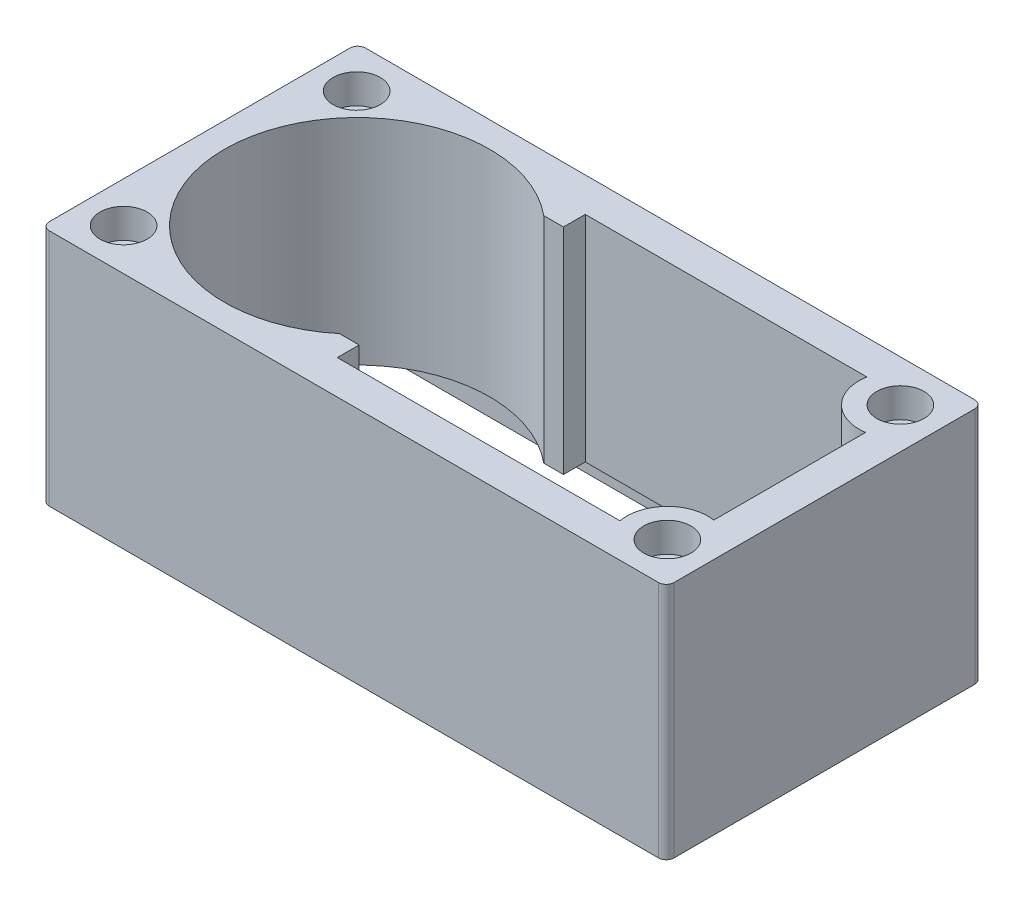
SolidWorks part; units mm, degrees
ref_plane "Front Plane" through (0, 0, 0) normal (0, 0, 1) x (1, 0, 0)
ref_plane "Top Plane" through (0, 0, 0) normal (0, 1, 0) x (1, 0, 0)
ref_plane "Right Plane" through (0, 0, 0) normal (1, 0, 0) x (0, 0, -1)
sketch "Sketch1" plane through (0, 0, 0) normal (0, 1, 0) x (1, 0, 0)
  line L1 (-20.193, 10.2235) -> (20.193, 10.2235)
  line L2 (-20.193, 10.2235) -> (-20.193, -10.2235)
  line L3 (-20.193, -10.2235) -> (20.193, -10.2235)
  line L4 (20.193, 10.2235) -> (20.193, -10.2235)
  line L5 (-20.193, 10.2235) -> (20.193, -10.2235) construction
  line L6 (-20.193, -10.2235) -> (20.193, 10.2235) construction
  point P0 (0, 0)
  dimension "D1" = 40.386
  dimension "D2" = 20.447
extrude "Boss-Extrude1" add sketch "Sketch1" along normal blind 15.4178
fillet "Fillet1" radius 0.508 4 edges at (20.193, 7.7089, 10.2235) (20.193, 7.7089, -10.2235) (-20.193, 7.7089, -10.2235) (-20.193, 7.7089, 10.2235)
hole_wizard "#2 Clearance Hole1" positions "Sketch4" profile "Sketch5" hole size "#2" standard "ANSI Inch" end condition up to next
sketch "Sketch4" plane through (0, 15.4178, 0) normal (0, 1, 0) x (1, 0, 0)
  line L1 (-17.5704, 7.5311) -> (17.5704, 7.5311)
  line L2 (-17.5704, 7.5311) -> (-17.5704, -7.5311)
  line L3 (-17.5704, -7.5311) -> (17.5704, -7.5311)
  line L4 (17.5704, 7.5311) -> (17.5704, -7.5311)
  line L5 (-17.5704, 7.5311) -> (17.5704, -7.5311) construction
  line L6 (-17.5704, -7.5311) -> (17.5704, 7.5311) construction
  point P2 (17.5704, -7.5311)
  point P81 (-17.5704, 7.5311)
  point P82 (-17.5704, -7.5311)
  point P83 (17.5704, 7.5311)
  point P97 (0, 0)
  dimension "D1" = 15.0622
  dimension "D2" = 35.1409
sketch "Sketch5" plane through (17.5704, 15.4178, 7.5311) normal (1, 0, 0) x (0, 0, 1)
  line L0 (0, 0) -> (0, 15.4178)
  line L1 (0, 15.4178) -> (1.1303, 15.4178)
  line L2 (1.1303, 15.4178) -> (1.1303, 0)
  line L5 (1.1303, 0) -> (0, 0)
  line L11 (0, -6.35) -> (0, 107.95) construction
  dimension "Thru Hole Dia." = 2.2606
  dimension "Thru Hole Depth" = 15.4178
sketch "Sketch6" plane through (0, 15.4178, 0) normal (0, 1, 0) x (1, 0, 0)
  circle A0 centre (-10.0147, 0) radius 8.5725
  circle A2 centre (-17.5704, 7.5311) radius 1.1303 construction
  dimension "D1" = 17.145
  dimension "D2" = 10.668
sketch "Sketch8" plane through (0, 15.4178, 0) normal (0, 1, 0) x (1, 0, 0)
  circle A0 centre (-17.5704, -7.5311) radius 1.524
  circle A1 centre (-17.5704, 7.5311) radius 1.524
  circle A2 centre (17.5704, 7.5311) radius 1.524
  circle A3 centre (17.5704, -7.5311) radius 1.524
  dimension "D1" = 3.048
extrude "Cut-Extrude2" cut sketch "Sketch8" against normal blind 1.905
sketch "Sketch10" plane through (0, 15.4178, 0) normal (0, 1, 0) x (1, 0, 0)
  line L0 (-4.5489, 6.604) -> (-4.5489, -6.604)
  line L1 (-4.5489, -6.604) -> (-3.2789, -6.604)
  line L2 (-3.2789, -6.604) -> (-3.2789, -8.0137)
  line L3 (-3.2789, -8.0137) -> (14.9927, -8.0137)
  line L5 (17.9835, -4.9413) -> (17.9835, 4.8706)
  line L7 (14.9217, 8.0137) -> (-3.2789, 8.0137)
  line L8 (-3.2789, 8.0137) -> (-3.2789, 6.604)
  line L9 (-3.2789, 6.604) -> (-4.5489, 6.604)
  line L10 (20.193, -9.7155) -> (20.193, 9.7155) construction
  line L11 (19.685, 10.2235) -> (-19.685, 10.2235) construction
  line L12 (5.8214, 8.0137) -> (5.8214, 10.2235) construction
  line L14 (17.9835, -0.0354) -> (20.193, 0) construction
  arc A2 (14.9217, 8.0137) -> (17.9835, 4.8706) centre (17.5704, 7.5311) ccw
  arc A3 (17.9835, -4.9413) -> (14.9927, -8.0137) centre (17.5704, -7.5311) ccw
  circle A4 centre (-10.0147, 0) radius 8.5725 construction
  point P2 (0, 0)
  point P3 (-1.7525, 5.4229)
  point P26 (0, 0)
  point P27 (0, 0)
  dimension "D1" = 13.208
  dimension "D2" = 2.2098
  dimension "D4" = 1.27
extrude "Cut-Extrude5" cut sketch "Sketch6" against normal through all contours A0
extrude "Cut-Extrude6" cut sketch "Sketch10" against normal through all contours L0 L1 L2 L3 A3 L5 A2 L7 L8 L9
sketch "Sketch11" plane through (0, 0, 0) normal (0, -1, 0) x (1, 0, 0)
  line L0 (18.9611, 8.9916) -> (-18.9611, 8.9916)
  line L1 (-18.9611, 8.9916) -> (-18.9611, -8.9916)
  line L2 (-18.9611, -8.9916) -> (18.9611, -8.9916)
  line L3 (18.9611, -8.9916) -> (18.9611, 8.9916)
  line L4 (20.193, -9.7155) -> (20.193, 9.7155)
  line L5 (19.685, 10.2235) -> (-19.685, 10.2235)
  line L6 (-20.193, 9.7155) -> (-20.193, -9.7155)
  line L7 (-19.685, -10.2235) -> (19.685, -10.2235)
  line L8 (20.193, -9.7155) -> (20.193, 9.7155)
  line L9 (19.685, 10.2235) -> (-19.685, 10.2235)
  line L10 (-20.193, 9.7155) -> (-20.193, -9.7155)
  line L11 (-19.685, -10.2235) -> (19.685, -10.2235)
  arc A0 (-18.9611, 8.9916) -> (-18.9611, 8.9916) centre (-18.9611, 8.9916) ccw
  arc A1 (-18.9611, -8.9916) -> (-18.9611, -8.9916) centre (-18.9611, -8.9916) ccw
  arc A2 (18.9611, -8.9916) -> (18.9611, -8.9916) centre (18.9611, -8.9916) ccw
  arc A3 (18.9611, 8.9916) -> (18.9611, 8.9916) centre (18.9611, 8.9916) ccw
  arc A4 (20.193, 9.7155) -> (19.685, 10.2235) centre (19.685, 9.7155) ccw
  arc A5 (-19.685, 10.2235) -> (-20.193, 9.7155) centre (-19.685, 9.7155) ccw
  arc A6 (-20.193, -9.7155) -> (-19.685, -10.2235) centre (-19.685, -9.7155) ccw
  arc A7 (19.685, -10.2235) -> (20.193, -9.7155) centre (19.685, -9.7155) ccw
  arc A8 (20.193, 9.7155) -> (19.685, 10.2235) centre (19.685, 9.7155) ccw
  arc A9 (-19.685, 10.2235) -> (-20.193, 9.7155) centre (-19.685, 9.7155) ccw
  arc A10 (-20.193, -9.7155) -> (-19.685, -10.2235) centre (-19.685, -9.7155) ccw
  arc A11 (19.685, -10.2235) -> (20.193, -9.7155) centre (19.685, -9.7155) ccw
  point P24 (0, 0)
  line M11 (-3.2789, -8.0137) -> (-3.2789, -6.604)
  line M12 (-3.2789, -6.604) -> (-4.5489, -6.604)
  arc M13 (-4.5489, -6.604) -> (-4.5489, 6.604) centre (-10.0147, 0) cw
  line M14 (-4.5489, 6.604) -> (-3.2789, 6.604)
  line M15 (-3.2789, 6.604) -> (-3.2789, 8.0137)
  line M16 (-3.2789, 8.0137) -> (14.9927, 8.0137)
  arc M17 (14.9927, 8.0137) -> (17.9835, 4.9413) centre (17.5704, 7.5311) ccw
  line M18 (17.9835, 4.9413) -> (17.9835, -4.8706)
  arc M19 (17.9835, -4.8706) -> (14.9217, -8.0137) centre (17.5704, -7.5311) ccw
  line M20 (14.9217, -8.0137) -> (-3.2789, -8.0137)
  circle M21 centre (17.5704, 7.5311) radius 1.1303
  circle M22 centre (-17.5704, -7.5311) radius 1.1303
  circle M23 centre (-17.5704, 7.5311) radius 1.1303
  circle M24 centre (17.5704, -7.5311) radius 1.1303
  dimension "D2" = 17.9832
  dimension "D1" = 0
extrude "Cut-Extrude7" cut sketch "Sketch11" against normal blind 1.5621 contours L2 L3 L0 L1 M20 M11 M12 M13 M14 M15 M16 M17 M18 M19 M21 M23 M24 M22
equation "\"D1@Boss-Extrude1\"=.86+.6"
